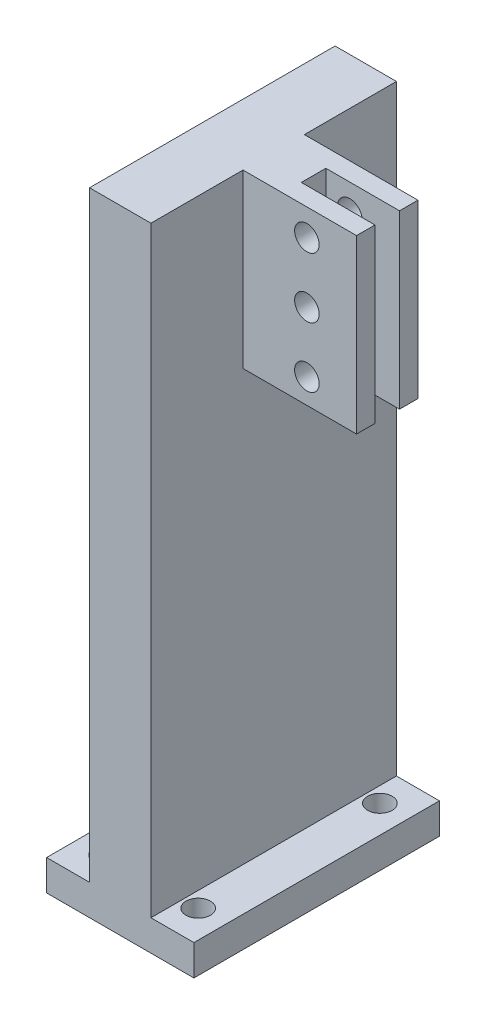
SolidWorks part; units mm, degrees
ref_plane "Front" through (0, 0, 0) normal (0, 0, 1) x (1, 0, 0)
ref_plane "Top" through (0, 0, 0) normal (0, 1, 0) x (1, 0, 0)
ref_plane "Right" through (0, 0, 0) normal (1, 0, 0) x (0, 0, -1)
sketch "草图1" plane through (0, 0, 0) normal (0, 1, 0) x (1, 0, 0)
  line L0 (0, 0) -> (0, -14.8) construction
  line L1 (-20, 20) -> (20, 20) construction
  line L2 (20, 20) -> (20, -20) construction
  line L3 (20, 0) -> (0, 0) construction
  line L4 (0, 0) -> (0, 20) construction
  line L5 (0, 20) -> (12, 20) construction
  line L6 (-20, 20) -> (-20, -20) construction
  line L7 (-20, -20) -> (20, -20) construction
  line L12 (0, -14.8) -> (7.5, -14.8) construction
  line L13 (0, -14.8) -> (-7.5, -14.8) construction
  line L14 (12, 20) -> (12, -20) construction
  line L15 (12, -20) -> (-12, -20)
  line L16 (12, -20) -> (12, 20)
  line L17 (12, 20) -> (-12, 20)
  line L18 (-12, -20) -> (-12, 20)
  circle A4 centre (7.5, -14.8) radius 2
  circle A5 centre (-7.5, -14.8) radius 2
  circle A6 centre (-7.5, 14.8) radius 2
  circle A7 centre (7.5, 14.8) radius 2
  point P13 (10, 0)
  point P14 (-10, 0)
  point P16 (-20, 0)
  point P22 (12, 0)
  point P26 (0, -20)
extrude "凸台-拉伸1" add sketch "草图1" along normal blind 5
sketch "草图8" plane through (0, 5, 0) normal (0, 1, 0) x (1, 0, 0)
  line L0 (0, 0) -> (5, 0) construction
  line L1 (0, 0) -> (-5, 0) construction
  line L2 (-5, 0) -> (-5, -20)
  line L3 (-12, -20) -> (12, -20) construction
  line L4 (-5, -20) -> (5, -20)
  line L5 (5, -20) -> (5, 20)
  line L6 (12, 20) -> (-12, 20) construction
  line L7 (5, 20) -> (-5, 20)
  line L8 (-5, 20) -> (-5, 0)
  line L9 (5, 20) -> (12, 20) construction
extrude "凸台-拉伸5" add sketch "草图8" along normal blind 98
sketch "草图10" plane through (5, 0, 0) normal (1, 0, 0) x (0, 0, -1)
  line L0 (0, 103) -> (5, 103) construction
  line L1 (-20, 103) -> (20, 103) construction
  line L2 (5, 103) -> (5, 75) construction
  line L3 (5, 75) -> (-5, 75) construction
  line L4 (-5, 75) -> (-5, 103) construction
  line L5 (-5, 103) -> (0, 103) construction
  line L6 (-5, 103) -> (5, 103)
  line L7 (5, 103) -> (5, 75)
  line L8 (5, 75) -> (-5, 75)
  line L9 (-5, 75) -> (-5, 103)
extrude "凸台-拉伸6" add sketch "草图10" along normal blind 18.5
sketch "草图12" plane through (0, 0, -5) normal (0, 0, -1) x (-1, 0, 0)
  line L0 (-23.5, 103) -> (-11.5, 103) construction
  line L1 (-23.5, 103) -> (-5, 103) construction
  line L2 (-17.5, 98.67) -> (-17.5, 88.85) construction
  line L3 (-17.5, 98.67) -> (-21.41, 98.67) construction
  line L4 (-17.5, 88.85) -> (-21.41, 88.85) construction
  line L5 (-21.41, 88.85) -> (-21.41, 79.03) construction
  line L6 (-11.5, 103) -> (-11.5, 98.67) construction
  line L7 (-11.5, 98.67) -> (-15.41, 98.67) construction
  line L8 (-15.41, 98.67) -> (-15.41, 88.85) construction
  line L9 (-15.41, 88.85) -> (-11.5, 88.85) construction
  line L10 (-11.5, 88.85) -> (-11.5, 79.03) construction
  line L11 (-11.5, 79.03) -> (-15.41, 79.03) construction
  line L12 (-11.5, 79.03) -> (-6.9723, 79.03) construction
  line L13 (-6.9723, 79.03) -> (-6.9723, 75) construction
  line L14 (-23.5, 75) -> (-5, 75) construction
  circle A3 centre (-15.41, 98.67) radius 2
  circle A4 centre (-15.41, 88.85) radius 2
  circle A5 centre (-15.41, 79.03) radius 2
extrude "切除-拉伸4" cut sketch "草图12" against normal blind 24.5
sketch "草图13" plane through (0, 0, 0) normal (0, 0, 1) x (1, 0, 0)
  line L0 (23.5, 103) -> (11.5, 103)
  line L1 (23.5, 103) -> (5, 103) construction
  line L5 (23.5, 75) -> (23.5, 103)
  line L6 (11.5, 103) -> (11.5, 75)
  line L7 (23.5, 75) -> (5, 75) construction
  line L8 (11.5, 75) -> (23.5, 75)
extrude "切除-拉伸5" cut sketch "草图13" against normal mid plane 4
